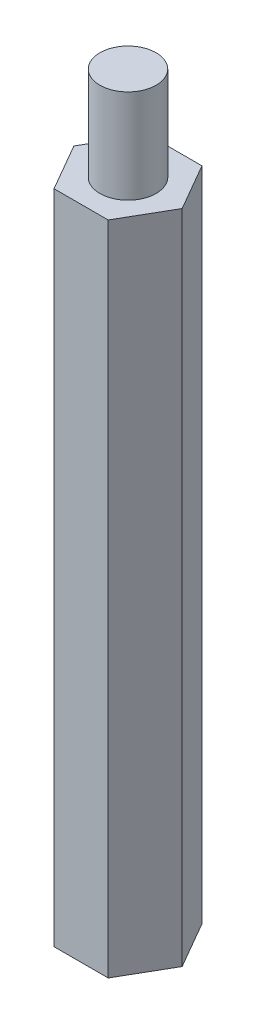
SolidWorks part; units mm, degrees
ref_plane "Front" through (0, 0, 0) normal (0, 0, 1) x (1, 0, 0)
ref_plane "Top" through (0, 0, 0) normal (0, 1, 0) x (1, 0, 0)
ref_plane "Right" through (0, 0, 0) normal (1, 0, 0) x (0, 0, -1)
sketch "草圖1" plane through (0, 0, 0) normal (0, 1, 0) x (1, 0, 0)
  line L1 (2.8868, 0) -> (1.4434, 2.5)
  line L2 (1.4434, 2.5) -> (-1.4434, 2.5)
  line L3 (-1.4434, 2.5) -> (-2.8868, 0)
  line L4 (-2.8868, 0) -> (-1.4434, -2.5)
  line L5 (-1.4434, -2.5) -> (1.4434, -2.5)
  line L6 (1.4434, -2.5) -> (2.8868, 0)
  circle A0 centre (0, 0) radius 2.5 construction
  dimension "D1" = 5
extrude "填料-伸長1" add sketch "草圖1" along normal blind 35
sketch "草圖2" plane through (0, 35, 0) normal (0, 1, 0) x (1, 0, 0)
  circle A0 centre (0, 0) radius 1.5
  dimension "D1" = 3
extrude "填料-伸長2" add sketch "草圖2" along normal blind 5
